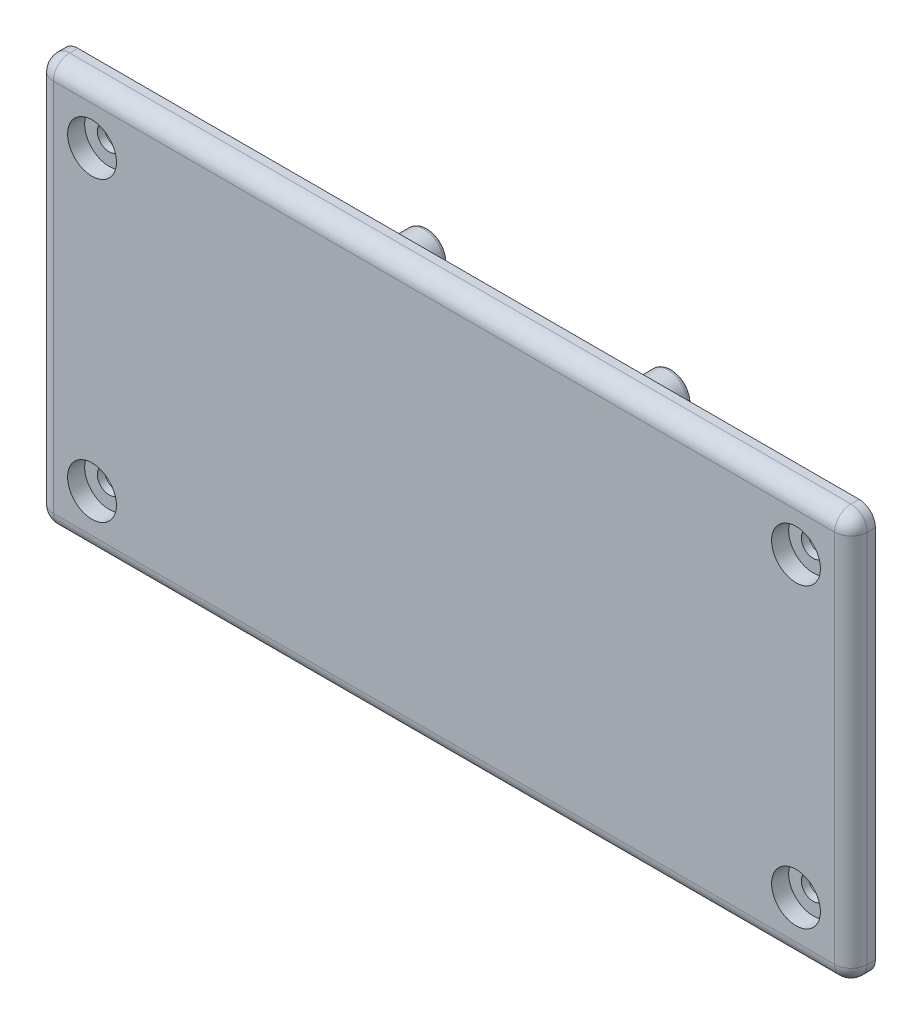
SolidWorks part; units mm, degrees
ref_plane "Front Plane" through (0, 0, 0) normal (0, 0, 1) x (1, 0, 0)
ref_plane "Top Plane" through (0, 0, 0) normal (0, 1, 0) x (1, 0, 0)
ref_plane "Right Plane" through (0, 0, 0) normal (1, 0, 0) x (0, 0, -1)
sketch "Sketch1" plane through (0, 0, 0) normal (0, 0, 1) x (1, 0, 0)
  line L4 (-48, -25) -> (48, -25)
  line L5 (50, -23) -> (50, 23)
  line L6 (48, 25) -> (-48, 25)
  line L7 (-50, 23) -> (-50, -23)
  line L8 (-48, -25) -> (48, -25)
  line L9 (50, -23) -> (50, 23)
  line L10 (48, 25) -> (-48, 25)
  line L11 (-50, 23) -> (-50, -23)
  arc A4 (48, -25) -> (50, -23) centre (48, -23) ccw
  arc A5 (50, 23) -> (48, 25) centre (48, 23) ccw
  arc A6 (-48, 25) -> (-50, 23) centre (-48, 23) ccw
  arc A7 (-50, -23) -> (-48, -25) centre (-48, -23) ccw
  arc A8 (48, -25) -> (50, -23) centre (48, -23) ccw
  arc A9 (50, 23) -> (48, 25) centre (48, 23) ccw
  arc A10 (-48, 25) -> (-50, 23) centre (-48, 23) ccw
  arc A11 (-50, -23) -> (-48, -25) centre (-48, -23) ccw
  dimension "D1" = 0
extrude "Boss-Extrude1" add sketch "Sketch1" along normal blind 3
fillet "Fillet1" radius 2 8 edges at (-50, 0, 3) (-49.4142, 24.4142, 3) (0, 25, 3) (49.4142, 24.4142, 3) (50, 0, 3) (49.4142, -24.4142, 3) (0, -25, 3) (-49.4142, -24.4142, 3)
sketch "Sketch2" plane through (0, 0, 0) normal (0, 0, -1) x (-1, 0, 0)
  line L0 (-25, -18.5) -> (-25, -21.5)
  line L1 (-35, -18.5) -> (-35, -21.5)
  line L2 (25, -18.5) -> (25, -21.5)
  line L3 (35, -18.5) -> (35, -21.5)
  line L4 (50, -23) -> (50, 23)
  line L5 (48, 25) -> (-48, 25)
  line L6 (-50, 23) -> (-50, -23)
  line L7 (-48, -25) -> (48, -25)
  line L8 (50, -23) -> (50, 23)
  line L9 (48, 25) -> (-48, 25)
  line L10 (-50, 23) -> (-50, -23)
  line L11 (-48, -25) -> (48, -25)
  line L12 (50, -23) -> (50, 23)
  line L13 (48, 25) -> (-48, 25)
  line L14 (-50, 23) -> (-50, -23)
  line L15 (-48, -25) -> (48, -25)
  line L16 (50, -23) -> (50, 23)
  line L17 (48, 25) -> (-48, 25)
  line L18 (-50, 23) -> (-50, -23)
  line L19 (-48, -25) -> (48, -25)
  line L20 (25, 18.5) -> (25, 21.5)
  line L21 (35, 18.5) -> (35, 21.5)
  line L22 (43.5, -10) -> (46.5, -10)
  line L23 (43.5, 10) -> (46.5, 10)
  line L24 (-46.5, -21.5) -> (46.5, -21.5)
  line L25 (-46.5, 21.5) -> (-46.5, -21.5)
  line L26 (46.5, 21.5) -> (-46.5, 21.5)
  line L27 (46.5, -21.5) -> (46.5, 21.5)
  line L28 (-46.5, -21.5) -> (46.5, -21.5)
  line L29 (-46.5, 21.5) -> (-46.5, -21.5)
  line L30 (46.5, 21.5) -> (-46.5, 21.5)
  line L31 (46.5, -21.5) -> (46.5, 21.5)
  line L32 (43.5, -18.5) -> (43.5, 18.5)
  line L33 (43.5, 18.5) -> (-43.5, 18.5)
  line L34 (-43.5, 18.5) -> (-43.5, -18.5)
  line L35 (-43.5, -18.5) -> (43.5, -18.5)
  line L36 (-43.5, -10) -> (-43.5, 10)
  line L37 (-25, 18.5) -> (-35, 18.5)
  line L38 (-43.5, 10) -> (-46.5, 10)
  line L39 (-43.5, 10) -> (-43.5, -10)
  line L40 (-43.5, -10) -> (-46.5, -10)
  line L41 (-46.5, 10) -> (-46.5, -10)
  line L42 (43.5, 0) -> (-46.5, 0) construction
  line L43 (-25, 18.5) -> (-35, 18.5)
  line L44 (-25, 18.5) -> (-25, 21.5)
  line L45 (-25, 21.5) -> (-35, 21.5)
  line L46 (-35, 18.5) -> (-35, 21.5)
  line L47 (0, 18.5) -> (0, -18.5) construction
  arc A4 (48, -25) -> (50, -23) centre (48, -23) ccw
  arc A5 (50, 23) -> (48, 25) centre (48, 23) ccw
  arc A6 (-48, 25) -> (-50, 23) centre (-48, 23) ccw
  arc A7 (-50, -23) -> (-48, -25) centre (-48, -23) ccw
  arc A8 (48, -25) -> (50, -23) centre (48, -23) ccw
  arc A9 (50, 23) -> (48, 25) centre (48, 23) ccw
  arc A10 (-48, 25) -> (-50, 23) centre (-48, 23) ccw
  arc A11 (-50, -23) -> (-48, -25) centre (-48, -23) ccw
  arc A12 (50, 23) -> (48, 25) centre (48, 23) ccw
  arc A13 (-48, 25) -> (-50, 23) centre (-48, 23) ccw
  arc A14 (-50, -23) -> (-48, -25) centre (-48, -23) ccw
  arc A15 (48, -25) -> (50, -23) centre (48, -23) ccw
  arc A16 (50, 23) -> (48, 25) centre (48, 23) ccw
  arc A17 (-48, 25) -> (-50, 23) centre (-48, 23) ccw
  arc A18 (-50, -23) -> (-48, -25) centre (-48, -23) ccw
  arc A19 (48, -25) -> (50, -23) centre (48, -23) ccw
  point P24 (-43.5, 0)
  point P29 (-30, 18.5)
  dimension "D5" = 20
  dimension "D6" = 10
  dimension "D7" = 11.5
  dimension "D1" = 0
  dimension "D2" = 0
  dimension "D3" = 3.5
  dimension "D4" = 3
extrude "Boss-Extrude2" add sketch "Sketch2" along normal blind 1.5 contours L46 L33 L44 L30 | L40 L34 L38 L29 | L35 L1 L28 L0 | L35 L2 L28 L3 | L32 L22 L31 L23 | L33 L21 L30 L20
fillet "Fillet2" radius 1 48 edges at (-30, 18.5, -1.5) (-25, 18.5, -0.75) (-35, 18.5, -0.75) (-35, 21.5, -0.75) (-25, 20, -1.5) (-25, 21.5, -0.75) (-35, 20, -1.5) (-30, 21.5, -1.5) (35, 20, -1.5) (35, 21.5, -0.75) (30, 18.5, -1.5) (35, 18.5, -0.75) (25, 18.5, -0.75) (25, 21.5, -0.75) (25, 20, -1.5) (30, 21.5, -1.5) (45, -10, -1.5) (46.5, -10, -0.75) (43.5, 0, -1.5) (43.5, -10, -0.75) (43.5, 10, -0.75) (46.5, 10, -0.75) (45, 10, -1.5) (46.5, 0, -1.5) (30, -18.5, -1.5) (25, -18.5, -0.75) (35, -18.5, -0.75) (35, -21.5, -0.75) (25, -20, -1.5) (25, -21.5, -0.75) (35, -20, -1.5) (30, -21.5, -1.5) (-30, -18.5, -1.5) (-35, -18.5, -0.75) (-25, -18.5, -0.75) (-25, -21.5, -0.75) (-35, -20, -1.5) (-35, -21.5, -0.75) (-25, -20, -1.5) (-30, -21.5, -1.5) (-43.5, 0, -1.5) (-43.5, 10, -0.75) (-43.5, -10, -0.75) (-46.5, -10, -0.75) (-45, 10, -1.5) (-46.5, 10, -0.75) (-45, -10, -1.5) (-46.5, 0, -1.5)
sketch "Sketch3" plane through (0, 0, 0) normal (0, 0, -1) x (-1, 0, 0)
  line L4 (50, -23) -> (50, 23)
  line L5 (48, 25) -> (-48, 25)
  line L6 (-50, 23) -> (-50, -23)
  line L7 (-48, -25) -> (48, -25)
  line L8 (50, -23) -> (50, 23)
  line L9 (48, 25) -> (-48, 25)
  line L10 (-50, 23) -> (-50, -23)
  line L11 (-48, -25) -> (48, -25)
  circle A0 centre (-15, -15) radius 3.0099 construction
  circle A1 centre (-15, 15) radius 3.0099 construction
  circle A2 centre (15, -15) radius 3.0099 construction
  circle A3 centre (15, 15) radius 3.0099 construction
  arc A4 (48, -25) -> (50, -23) centre (48, -23) ccw
  arc A5 (50, 23) -> (48, 25) centre (48, 23) ccw
  arc A6 (-48, 25) -> (-50, 23) centre (-48, 23) ccw
  arc A7 (-50, -23) -> (-48, -25) centre (-48, -23) ccw
  arc A8 (48, -25) -> (50, -23) centre (48, -23) ccw
  arc A9 (50, 23) -> (48, 25) centre (48, 23) ccw
  arc A10 (-48, 25) -> (-50, 23) centre (-48, 23) ccw
  arc A11 (-50, -23) -> (-48, -25) centre (-48, -23) ccw
  circle A12 centre (-15, -15) radius 3.0099 construction
  circle A13 centre (-15, 15) radius 3.0099 construction
  circle A14 centre (15, -15) radius 3.0099 construction
  circle A15 centre (15, 15) radius 3.0099 construction
  circle A16 centre (-15, 15) radius 2.5099
  circle A17 centre (-15, -15) radius 2.5099
  circle A18 centre (15, -15) radius 2.5099
  circle A19 centre (15, 15) radius 2.5099
  dimension "D1" = 0
  dimension "D2" = 0.5
extrude "Boss-Extrude3" add sketch "Sketch3" along normal blind 10 contours A17 | A16 | A18 | A19
fillet "Fillet3" radius 0.5 4 edges at (12.4901, 15, -10) (-17.5099, -15, -10) (-17.5099, 15, -10) (12.4901, -15, -10)
sketch "Sketch4" plane through (0, 0, 3) normal (0, 0, 1) x (1, 0, 0)
  line L0 (-47, 14.5) -> (-39.5001, 14.5) construction
  line L1 (-39.5001, 22) -> (-39.5001, 14.5) construction
  line L2 (47, -14.5) -> (39.5001, -14.5) construction
  line L3 (39.5001, -22) -> (39.5001, -14.5) construction
  line L4 (48, 23) -> (-48, 23)
  line L5 (-48, 23) -> (-48, -23)
  line L6 (-48, -23) -> (48, -23)
  line L7 (48, -23) -> (48, 23)
  line L8 (48, 23) -> (-48, 23)
  line L9 (-48, 23) -> (-48, -23)
  line L10 (-48, -23) -> (48, -23)
  line L11 (48, -23) -> (48, 23)
  line L12 (-47, -22) -> (47, -22)
  line L13 (47, -22) -> (47, 22)
  line L14 (47, 22) -> (-47, 22)
  line L15 (-47, 22) -> (-47, -22)
  line L16 (-47, -22) -> (47, -22)
  line L17 (47, -22) -> (47, 22)
  line L18 (47, 22) -> (-47, 22)
  line L19 (-47, 22) -> (-47, -22)
  line L20 (47, 14.5) -> (39.5001, 14.5) construction
  line L21 (39.5001, 22) -> (39.5001, 14.5) construction
  line L22 (47, 0) -> (-47, 0) construction
  line L23 (0, -22) -> (0, 22) construction
  line L24 (-47, -14.5) -> (-39.5001, -14.5) construction
  line L25 (-39.5001, -22) -> (-39.5001, -14.5) construction
  line L26 (-47, 14.5) -> (-39.5001, 14.5)
  line L27 (-39.5001, 22) -> (-39.5001, 14.5)
  line L28 (47, -14.5) -> (39.5001, -14.5)
  line L29 (39.5001, -22) -> (39.5001, -14.5)
  line L30 (47, 14.5) -> (39.5001, 14.5)
  line L31 (39.5001, 22) -> (39.5001, 14.5)
  line L32 (47, 0) -> (-47, 0)
  line L33 (0, -22) -> (0, 22)
  line L34 (-47, -14.5) -> (-39.5001, -14.5)
  line L35 (-39.5001, -22) -> (-39.5001, -14.5)
  circle A1 centre (-43.2501, -18.25) radius 1.025
  circle A2 centre (-43.2501, -18.25) radius 1.025
  circle A3 centre (43.2501, -18.25) radius 1.025
  circle A4 centre (43.2501, -18.25) radius 1.025
  circle A5 centre (43.2501, 18.25) radius 1.025
  circle A6 centre (43.2501, 18.25) radius 1.025
  circle A7 centre (-43.2501, 18.25) radius 1.025
  circle A8 centre (-43.2501, 18.25) radius 1.025
  dimension "D1" = 0
  dimension "D2" = 0
  dimension "D3" = 0
  dimension "D4" = 0
  dimension "D5" = 0
  dimension "D6" = 0
hole_wizard "CBORE for M2.5 Pan Head Machine Screw1" positions "3DSketch2" profile "Sketch6" counterbore size "M2.5" standard "ANSI Metric"
sketch3d "3DSketch2"
  point P0 (43.2501, -18.25, 3)
  point P3 (43.2501, 18.25, 3)
  point P6 (-43.2501, -18.25, 3)
  point P9 (-43.2501, 18.25, 3)
sketch "Sketch6" plane through (43.2501, -18.25, 3) normal (1, 0, 0) x (0, -1, 0)
  line L0 (0, 0) -> (0, 7.2212)
  line L1 (0, 7.2212) -> (1.45, 6.35)
  line L2 (1.45, 6.35) -> (1.45, 2.1)
  line L3 (1.45, 2.1) -> (3, 2.1)
  line L4 (3, 2.1) -> (3, 0)
  line L5 (3, 0) -> (0, 0)
  line L10 (0, 7.2212) -> (-1.45, 6.35) construction
  line L11 (0, -6.35) -> (0, 107.95) construction
  dimension "Hole Dia." = 2.9
  dimension "Hole Depth" = 6.35
  dimension "C'Bore Dia." = 6
  dimension "C'Bore Depth" = 2.1
  dimension "Drill Angle" = 118
